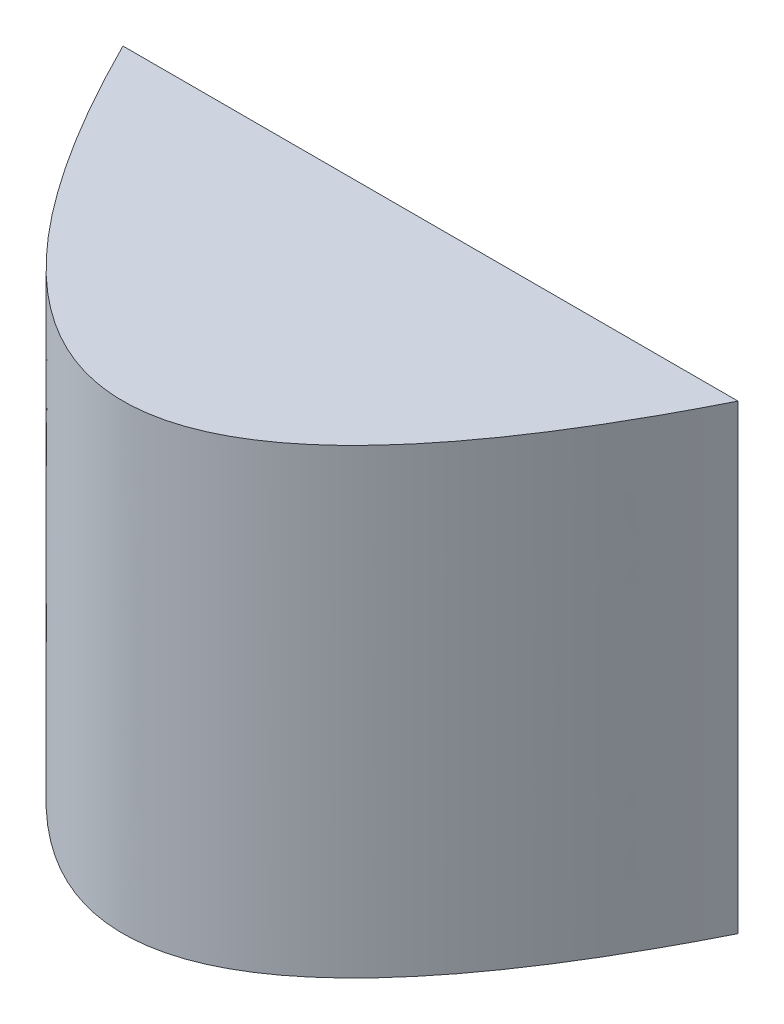
SolidWorks part; units mm, degrees
material "Custom Plastic (2)"
ref_plane "Front Plane" through (0, 0, 0) normal (0, 0, 1) x (1, 0, 0)
ref_plane "Top Plane" through (0, 0, 0) normal (0, 1, 0) x (1, 0, 0)
ref_plane "Right Plane" through (0, 0, 0) normal (1, 0, 0) x (0, 0, -1)
sketch "Sketch1" plane through (0, 0, 0) normal (0, 1, 0) x (1, 0, 0)
  line L0 (-200, 0) -> (200, 0)
  spline S0 degree 2 poles (-225.2396, 53.6645) (0, -453.6645) (225.2396, 53.6645) knots 0 0 0 1 1 1 construction
  spline S1 degree 2 poles (-200, 0) (0, -400) (200, 0) knots 0.056028 0.056028 0.056028 0.943972 0.943972 0.943972
extrude "Boss-Extrude1" add sketch "Sketch1" along normal blind 300
